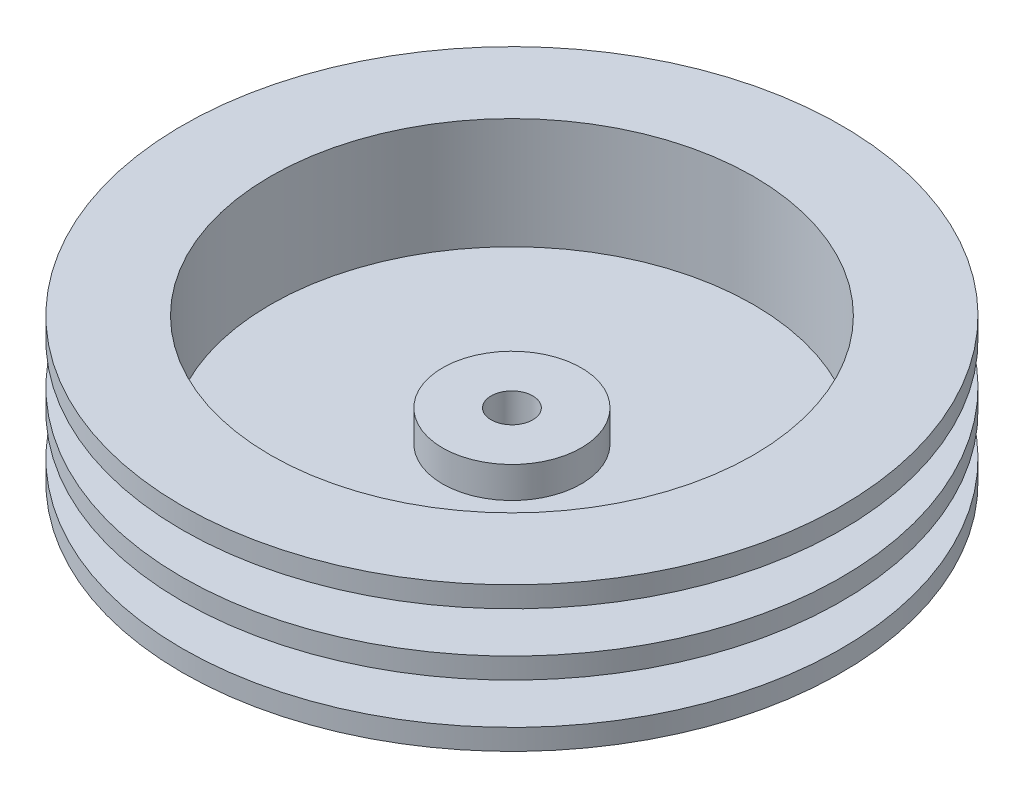
SolidWorks part; units mm, degrees
material "Delrin 2700 NC010, Low Viscosity Acetal Copolymer (SS)"
ref_plane "Front Plane" through (0, 0, 0) normal (0, 0, 1) x (1, 0, 0)
ref_plane "Top Plane" through (0, 0, 0) normal (0, 1, 0) x (1, 0, 0)
ref_plane "Right Plane" through (0, 0, 0) normal (1, 0, 0) x (0, 0, -1)
sketch "Sketch1" plane through (0, 0, 0) normal (0, 0, 1) x (1, 0, 0)
  line L0 (0, -430.3278) -> (0, 21086.0609) construction
  line L1 (0, 0) -> (23.75, 0)
  line L2 (23.75, 0) -> (23.75, 1.5)
  line L3 (23.75, 1.5) -> (18.9, 1.5)
  line L4 (18.9, 1.5) -> (18.9, 4.45)
  line L5 (18.9, 4.45) -> (23.75, 4.45)
  line L6 (23.75, 4.45) -> (23.75, 5.95)
  line L7 (23.75, 5.95) -> (18.9, 5.95)
  line L8 (18.9, 5.95) -> (18.9, 8.9)
  line L9 (18.9, 8.9) -> (23.75, 8.9)
  line L10 (23.75, 8.9) -> (23.75, 10.4)
  line L11 (23.75, 10.4) -> (17.4, 10.4)
  line L12 (17.4, 10.4) -> (17.4, 2.4)
  line L13 (17.4, 2.4) -> (5, 2.4)
  line L14 (5, 2.4) -> (5, 4.65)
  line L15 (5, 4.65) -> (0, 4.65)
  line L16 (0, 4.65) -> (0, 0)
  line L17 (18.9, 4.45) -> (17.4, 4.45) construction
  dimension "D1" = 23.75
  dimension "D2" = 10.4
  dimension "D3" = 1.5
  dimension "D4" = 17.4
  dimension "D5" = 8
  dimension "D6" = 2.25
  dimension "D7" = 5
revolve "Revolve1" add sketch "Sketch1" angle 360 about L16
sketch "Sketch2" plane through (0, 4.65, 0) normal (0, 1, 0) x (1, 0, 0)
  circle A0 centre (0, 0) radius 1.5
  dimension "D1" = 3
extrude "Cut-Extrude1" cut sketch "Sketch2" against normal through all
